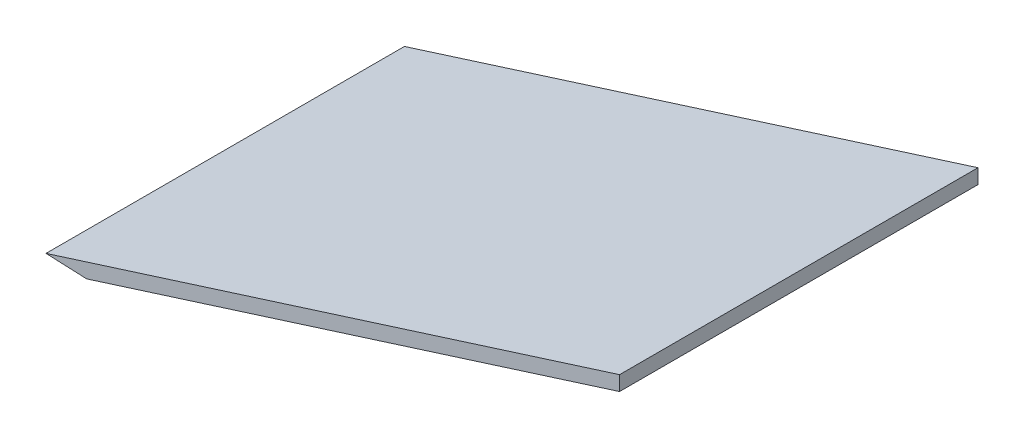
SolidWorks part; units mm, degrees
ref_plane "Front Plane" through (0, 0, 0) normal (0, 0, 1) x (1, 0, 0)
ref_plane "Top Plane" through (0, 0, 0) normal (0, 1, 0) x (1, 0, 0)
ref_plane "Right Plane" through (0, 0, 0) normal (1, 0, 0) x (0, 0, -1)
sketch "Sketch2" plane through (0, 0, 0) normal (0, 0, 1) x (1, 0, 0)
  line L0 (259.1, -157.7714) -> (259.1, -154.6243)
  line L1 (259.1, -157.7714) -> (144.6122, -194.0515)
  line L2 (259.1, -154.6243) -> (135.8826, -193.6708)
  line L6 (135.8826, -193.6708) -> (144.6122, -194.0515)
  line L12 (259.1, -154.6243) -> (259.1001, 3.8232) construction
  line L16 (-17.6214, -76.2978) -> (286.6295, -308.9357) construction
  line L17 (-14.5843, -72.3259) -> (289.6666, -304.9638) construction
  circle A1 centre (277.9804, -217.3514) radius 62.5 construction
  dimension "D1" = 3
extrude "Boss-Extrude1" add sketch "Sketch2" along normal up to surface (77 mm away)
